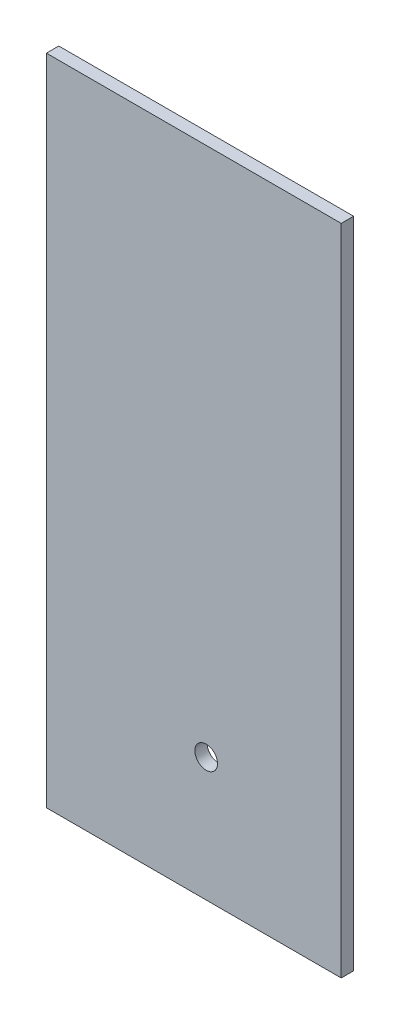
SolidWorks part; units mm, degrees
material "Perspex (TM) GS Acrylic Cast Sheet"
ref_plane "Front Plane" through (0, 0, 0) normal (0, 0, 1) x (1, 0, 0)
ref_plane "Top Plane" through (0, 0, 0) normal (0, 1, 0) x (1, 0, 0)
ref_plane "Right Plane" through (0, 0, 0) normal (1, 0, 0) x (0, 0, -1)
sketch "Sketch1" plane through (0, 0, 0) normal (0, 0, 1) x (1, 0, 0)
  line L1 (-71.5, -158.5) -> (71.5, -158.5)
  line L2 (-71.5, -158.5) -> (-71.5, 158.5)
  line L3 (-71.5, 158.5) -> (71.5, 158.5)
  line L4 (71.5, -158.5) -> (71.5, 158.5)
  line L5 (-71.5, -158.5) -> (71.5, 158.5) construction
  line L6 (-71.5, 158.5) -> (71.5, -158.5) construction
  point P0 (0, 0)
  dimension "D1" = 143
  dimension "D2" = 317
extrude "Boss-Extrude1" add sketch "Sketch1" along normal blind 6
sketch "Sketch2" plane through (0, 0, 6) normal (0, 0, 1) x (1, 0, 0)
  line L0 (6, -158.5) -> (6, -98.5) construction
  line L2 (-71.5, -158.5) -> (71.5, -158.5) construction
  circle A0 centre (6, -98.5) radius 5.5
  point P10 (0, -158.5)
  dimension "D2" = 11
  dimension "D1" = 60
  dimension "D3" = 6
extrude "Cut-Extrude1" cut sketch "Sketch2" against normal through all
equation "\"PCLength\"= 143mm'Length across I/O from PS to GPU"
equation "\"PCWidth\"= 340mm'Distance of longest part parallel to GPU(ussually GPU)"
equation "\"PCHeight\"= 190mm'Tallest point with mobo laying flat"
equation "\"WallThickness\"= 9mm'Thickness of each outer tank wall"
equation "\"ThermoBarrierThickness\"= 6mm'Thickness of barrier between hot side and cold side"
equation "\"HotSideGap\"= 15mm'Space in the hot side that hot fluid flows into"
equation "\"PCClearance\"= 40mm'Clearance from top of tank to top of PC"
equation "\"RadiatorHeight\"= 277.37mm'Final Height from ground of radiators"
equation "\"D1@Sketch1\"=\"PCLength\""
equation "\"D2@Sketch1\"=\"RadiatorHeight\" + 40 - 0.37"
equation "\"D1@Boss-Extrude1\"=\"ThermoBarrierThickness\""
